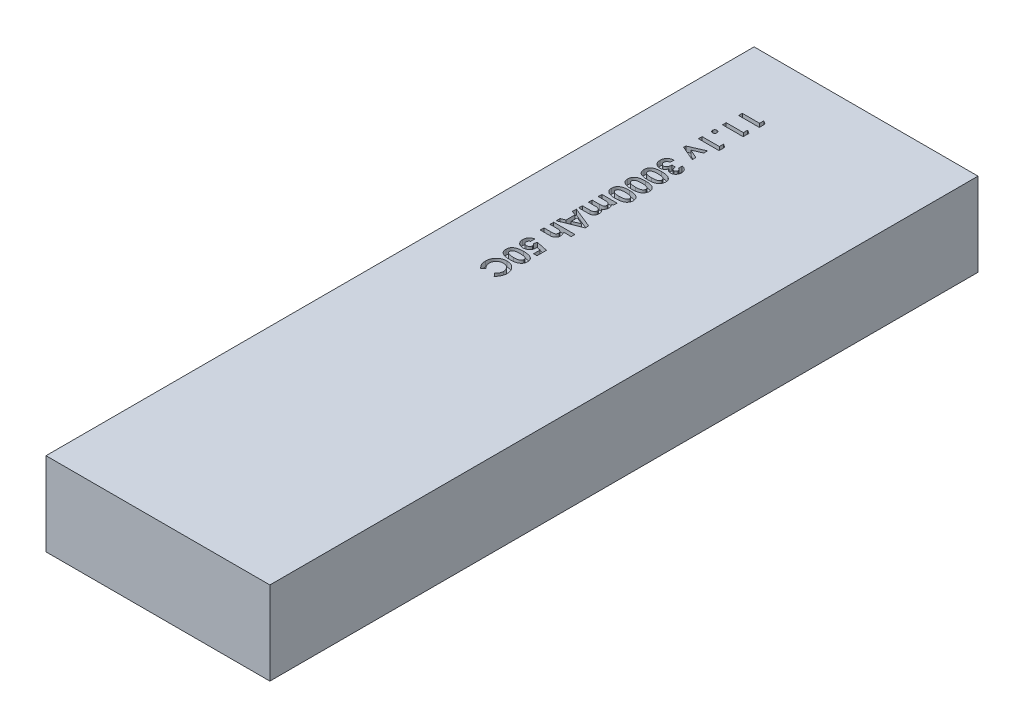
SolidWorks part; units mm, degrees
ref_plane "Front Plane" through (0, 0, 0) normal (0, 0, 1) x (1, 0, 0)
ref_plane "Top Plane" through (0, 0, 0) normal (0, 1, 0) x (1, 0, 0)
ref_plane "Right Plane" through (0, 0, 0) normal (1, 0, 0) x (0, 0, -1)
sketch "Sketch1" plane through (0, 0, 0) normal (0, 1, 0) x (1, 0, 0)
  line L1 (-21.5, 68) -> (21.5, 68)
  line L2 (-21.5, 68) -> (-21.5, -68)
  line L3 (-21.5, -68) -> (21.5, -68)
  line L4 (21.5, 68) -> (21.5, -68)
  line L5 (-21.5, 68) -> (21.5, -68) construction
  line L6 (-21.5, -68) -> (21.5, 68) construction
  point P0 (0, 0)
  dimension "D1" = 136
  dimension "D2" = 43
extrude "Boss-Extrude1" add sketch "Sketch1" along normal blind 16
sketch "Sketch6" plane through (0, 16, 0) normal (0, 1, 0) x (1, 0, 0)
  line L0 (-11.5748, 57.0882) -> (-11.5748, -8.5025) construction
  text T0 "<b>11.1v 3000mAh 50C</b>" font "Century Gothic" height in points 15
extrude "Cut-Extrude3" cut sketch "Sketch6" against normal blind 1
